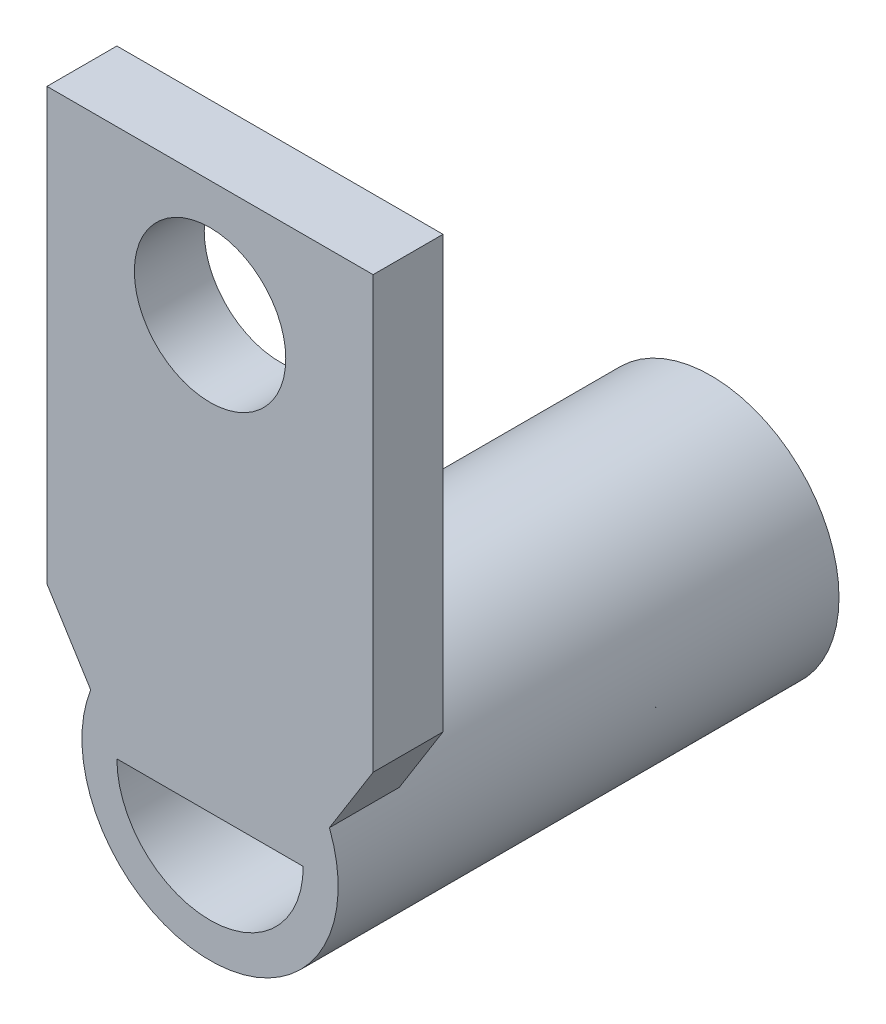
SolidWorks part; units mm, degrees
material "铜"
ref_plane "前视基准面" through (0, 0, 0) normal (0, 0, 1) x (1, 0, 0)
ref_plane "上视基准面" through (0, 0, 0) normal (0, 1, 0) x (1, 0, 0)
ref_plane "右视基准面" through (0, 0, 0) normal (1, 0, 0) x (0, 0, -1)
other "Configuration Table"
sketch "草图1" plane through (0, 0, 0) normal (0, 0, 1) x (1, 0, 0)
  circle A0 centre (0, 0) radius 5.5
  circle A1 centre (0, 0) radius 4
  dimension "D1" = 11
  dimension "D2" = 8
extrude "凸台-拉伸1" add sketch "草图1" along normal blind 21.5
sketch "草图2" plane through (0, 0, 0) normal (0, 1, 0) x (1, 0, 0)
  line L1 (-7, -18.5) -> (7, -18.5)
  line L2 (-7, -18.5) -> (-7, -21.5)
  line L3 (-7, -21.5) -> (7, -21.5)
  line L4 (7, -18.5) -> (7, -21.5)
  line L5 (0, 0) -> (0, -21.5) construction
  line L6 (5.5, 0) -> (-5.5, 0) construction
  line L7 (-5.5, -21.5) -> (5.5, -21.5) construction
  dimension "D1" = 3
  dimension "D2" = 14
extrude "凸台-拉伸2" add sketch "草图2" along normal blind 23.5
sketch "草图3" plane through (0, 0, 18.5) normal (0, 0, -1) x (-1, 0, 0)
  line L0 (0, 23.5) -> (0, 0) construction
  line L1 (-7, 23.5) -> (7, 23.5) construction
  line L2 (-4, 0) -> (4, 0) construction
  line L4 (-7, 23.5) -> (-7, 0) construction
  line L5 (-7, 5) -> (-7, 0)
  line L6 (-7, 0) -> (-5.5, 0)
  line L8 (7, 23.5) -> (7, 0) construction
  line L9 (7, 5) -> (7, 0)
  line L10 (7, 0) -> (5.5, 0)
  line L11 (-7, 5) -> (7, 5) construction
  line L12 (-7, 5) -> (-5.1235, 2)
  line L13 (5.1235, 2) -> (7, 5)
  line L14 (-5.1235, 2) -> (5.1235, 2) construction
  circle A0 centre (0, 18.5) radius 3.25
  arc A2 (5.5, 0) -> (-5.5, 0) centre (0, 0) ccw construction
  circle A3 centre (0, 0) radius 5.5 construction
  circle A4 centre (0, 0) radius 5.5
  line M3 (-7, 23.5) -> (-7, 0)
  arc M4 (-5.5, 0) -> (5.5, 0) centre (0, 0) cw
  line M5 (7, 0) -> (7, 23.5)
  line M7 (-7, 0) -> (-5.5, 0)
  line M8 (5.5, 0) -> (7, 0)
  dimension "D1" = 6.5
  dimension "D2" = 5
  dimension "D3" = 5
  dimension "D4" = 2
extrude "切除-拉伸1" cut sketch "草图3" against normal blind 10 contours A0 | L12 M3 M7 M4 | L13 M4 M8 M5
